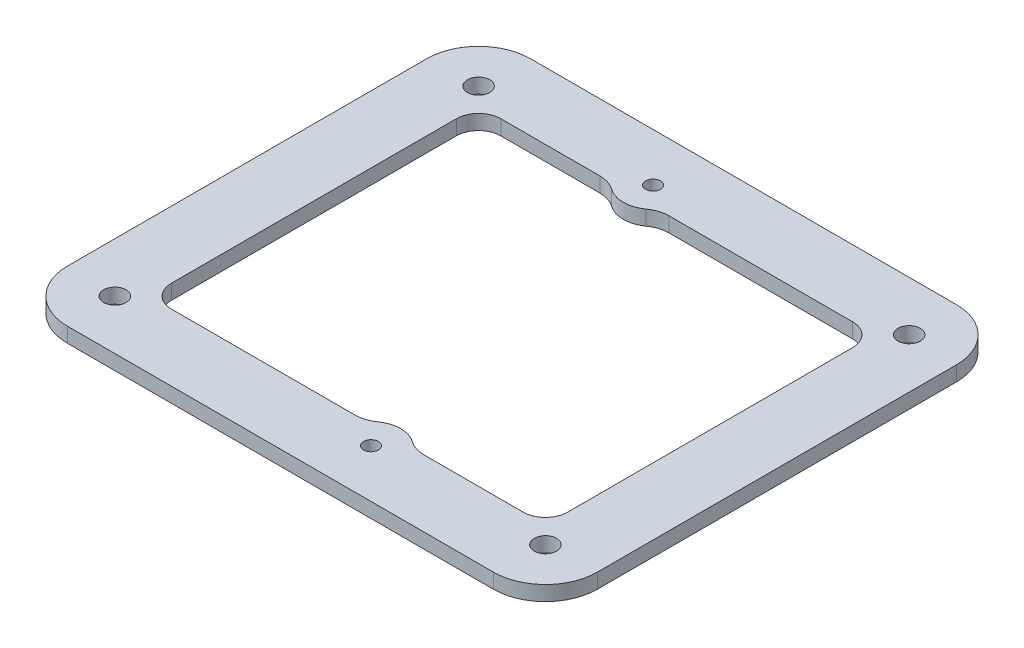
SolidWorks part; units mm, degrees
ref_plane "Front" through (0, 0, 0) normal (0, 0, 1) x (1, 0, 0)
ref_plane "Top" through (0, 0, 0) normal (0, 1, 0) x (1, 0, 0)
ref_plane "Right" through (0, 0, 0) normal (1, 0, 0) x (0, 0, -1)
sketch "草圖2" plane through (0, 0, 0) normal (0, 1, 0) x (-1, 0, 0)
  line L0 (-70.4577, 0) -> (70.2215, 0) construction
  line L1 (0, 52.2359) -> (0, -52.5789) construction
  line L2 (5.7, -24.7) -> (-5.7, 24.7) construction
  line L3 (23.6967, -31.1967) -> (-23.6967, -31.1967)
  line L4 (23.6967, -22.1967) -> (10.3591, -22.1967)
  line L5 (26.6967, -19.1967) -> (26.6967, 19.1967)
  line L6 (23.6967, 22.1967) -> (-1.0409, 22.1967)
  line L7 (-26.6967, -19.1967) -> (-26.6967, 19.1967)
  line L8 (26.6967, -22.1967) -> (-26.6967, 22.1967) construction
  line L9 (26.6967, 22.1967) -> (-26.6967, -22.1967) construction
  line L10 (-35.6967, -19.1967) -> (-35.6967, 19.1967)
  line L11 (23.6967, 31.1967) -> (-23.6967, 31.1967)
  line L12 (35.6967, -19.1967) -> (35.6967, 19.1967)
  line L13 (35.6967, 19.1967) -> (26.6967, 19.1967) construction
  line L14 (23.6967, 31.1967) -> (23.6967, 22.1967) construction
  line L15 (5.7, -36.2246) -> (5.7, -13.1754) construction
  line L16 (-5.7, 34.3093) -> (-5.7, 15.0907) construction
  line L17 (23.6967, -22.1967) -> (-23.6967, -22.1967) construction
  line L18 (1.0409, -22.1967) -> (-23.6967, -22.1967)
  line L19 (-23.6967, -31.1967) -> (-35.6967, -31.1967)
  line L20 (23.6967, 22.1967) -> (-23.6967, 22.1967) construction
  line L21 (-10.3591, 22.1967) -> (-23.6967, 22.1967)
  line L22 (-35.6967, 19.1967) -> (-35.6967, 31.1967)
  line L23 (-35.6967, -19.1967) -> (-35.6967, -31.1967)
  line L24 (-23.6967, 31.1967) -> (-35.6967, 31.1967)
  line L25 (23.6967, 31.1967) -> (35.6967, 31.1967)
  line L26 (35.6967, 19.1967) -> (35.6967, 31.1967)
  line L27 (35.6967, -19.1967) -> (35.6967, -31.1967)
  line L28 (23.6967, -31.1967) -> (35.6967, -31.1967)
  arc A0 (-26.6967, -19.1967) -> (-23.6967, -22.1967) centre (-23.6967, -19.1967) ccw
  arc A1 (26.6967, 19.1967) -> (23.6967, 22.1967) centre (23.6967, 19.1967) ccw
  arc A2 (23.6967, -22.1967) -> (26.6967, -19.1967) centre (23.6967, -19.1967) ccw
  circle A3 centre (29, 24.5) radius 1.5
  circle A4 centre (29, -24.5) radius 1.5
  circle A5 centre (-29, 24.5) radius 1.5
  circle A6 centre (-29, -24.5) radius 1.5
  circle A7 centre (5.7, -24.7) radius 1
  circle A8 centre (-5.7, 24.7) radius 1
  arc A9 (-23.6967, 22.1967) -> (-26.6967, 19.1967) centre (-23.6967, 19.1967) ccw
  arc A10 (-35.6967, -19.1967) -> (-23.6967, -31.1967) centre (-23.6967, -19.1967) ccw construction
  arc A11 (-23.6967, 31.1967) -> (-35.6967, 19.1967) centre (-23.6967, 19.1967) ccw construction
  arc A12 (35.6967, 19.1967) -> (23.6967, 31.1967) centre (23.6967, 19.1967) ccw construction
  arc A13 (23.6967, -31.1967) -> (35.6967, -19.1967) centre (23.6967, -19.1967) ccw construction
  arc A14 (26.6967, 19.1967) -> (23.6967, 22.1967) centre (23.6967, 19.1967) ccw construction
  arc A15 (31.1967, 19.1967) -> (23.6967, 26.6967) centre (23.6967, 19.1967) ccw construction
  arc A16 (8.0295, -21.4483) -> (3.3705, -21.4483) centre (5.7, -24.7) ccw
  arc A17 (8.0295, -21.4483) -> (10.3591, -22.1967) centre (10.3591, -18.1967) ccw
  arc A18 (3.3705, -21.4483) -> (1.0409, -22.1967) centre (1.0409, -18.1967) cw
  arc A19 (-3.3705, 21.4483) -> (-8.0295, 21.4483) centre (-5.7, 24.7) cw
  arc A20 (-3.3705, 21.4483) -> (-1.0409, 22.1967) centre (-1.0409, 18.1967) cw
  arc A21 (-8.0295, 21.4483) -> (-10.3591, 22.1967) centre (-10.3591, 18.1967) ccw
  point P4 (0, 0)
  point P7 (0, 0)
  point P23 (0, 0)
  point P25 (0, 0)
  point P31 (29, 24.5)
  point P56 (31.1967, 19.1967)
  point P58 (23.6967, 26.6967)
  point P60 (5.7, -24.7)
  point P68 (-5.7, 24.7)
  dimension "D6" = 3
  dimension "D7" = 2
  dimension "D8" = 3
  dimension "D10" = 4
  dimension "D11" = 4
  dimension "D1" = 49
  dimension "D2" = 58
  dimension "D4" = 11.4
  dimension "D5" = 49.4
  dimension "D9" = 9
  dimension "D3" = 2
extrude "填料-伸長1" add sketch "草圖2" along normal blind 2
fillet "圓角1" radius 7 4 edges at (35.6967, 1, -31.1967) (-35.6967, 1, -31.1967) (35.6967, 1, 31.1967) (-35.6967, 1, 31.1967)
